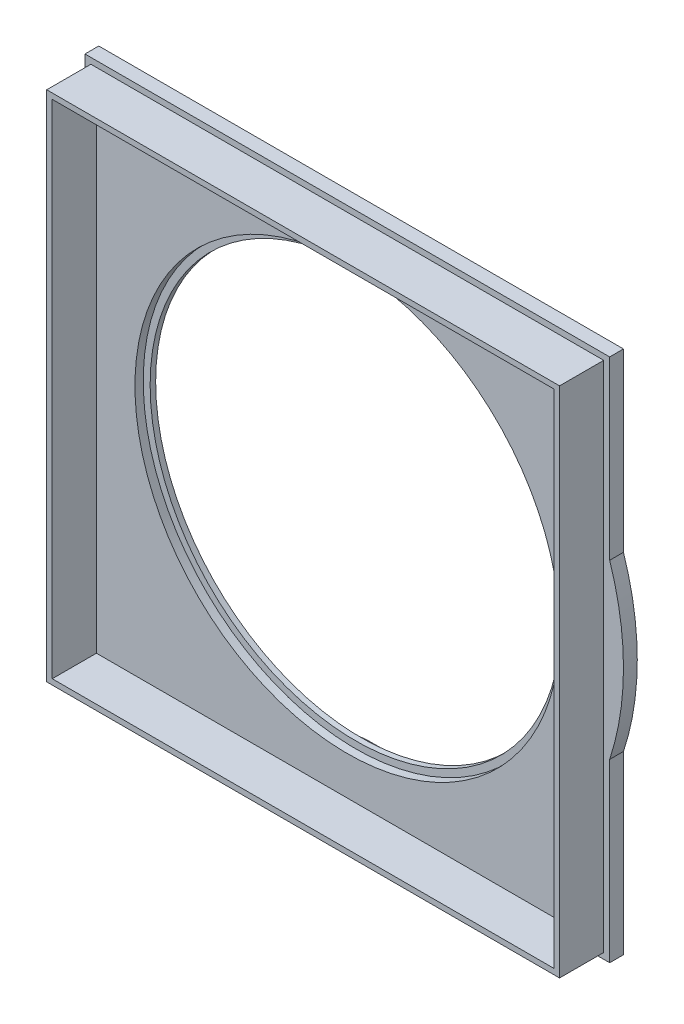
SolidWorks part; units mm, degrees
ref_plane "Alzado" through (0, 0, 0) normal (0, 0, 1) x (1, 0, 0)
ref_plane "Planta" through (0, 0, 0) normal (0, 1, 0) x (1, 0, 0)
ref_plane "Vista lateral" through (0, 0, 0) normal (1, 0, 0) x (0, 0, -1)
sketch "Croquis1" plane through (0, 0, 0) normal (0, 0, 1) x (1, 0, 0)
  line L1 (-46.425, -46.425) -> (46.425, -46.425)
  line L2 (-46.425, -46.425) -> (-46.425, 46.425)
  line L3 (-46.425, 46.425) -> (46.425, 46.425)
  line L4 (46.425, -46.425) -> (46.425, 46.425)
  line L5 (-46.425, -46.425) -> (46.425, 46.425) construction
  line L6 (-46.425, 46.425) -> (46.425, -46.425) construction
  circle A0 centre (0, 0) radius 37.2
  point P0 (0, 0)
  dimension "D2" = 74.4
  dimension "D1" = 92.85
extrude "Saliente-Extruir1" add sketch "Croquis1" along normal blind 2.5
sketch "Croquis2" plane through (0, 0, 2.5) normal (0, 0, 1) x (1, 0, 0)
  line L4 (45.425, -45.425) -> (45.425, 45.425)
  line L5 (45.425, 45.425) -> (-45.425, 45.425)
  line L6 (-45.425, 45.425) -> (-45.425, -45.425)
  line L7 (-45.425, -45.425) -> (45.425, -45.425)
  line L8 (46.425, -46.425) -> (46.425, 46.425)
  line L9 (46.425, 46.425) -> (-46.425, 46.425)
  line L10 (-46.425, 46.425) -> (-46.425, -46.425)
  line L11 (-46.425, -46.425) -> (46.425, -46.425)
  line L12 (46.425, -46.425) -> (46.425, 46.425)
  line L13 (46.425, 46.425) -> (-46.425, 46.425)
  line L14 (-46.425, 46.425) -> (-46.425, -46.425)
  line L15 (-46.425, -46.425) -> (46.425, -46.425)
  dimension "D1" = 0
  dimension "D2" = 1
extrude "Saliente-Extruir2" add sketch "Croquis2" along normal blind 8
sketch "Croquis3" plane through (0, 0, 0) normal (0, 0, -1) x (-1, 0, 0)
  line L4 (-47.5, 15.6125) -> (-47.5, 47.5)
  line L5 (-47.5, -47.5) -> (47.5, -47.5)
  line L6 (-47.5, -47.5) -> (-47.5, -15.6125)
  line L7 (-47.5, 47.5) -> (47.5, 47.5)
  line L8 (47.5, -47.5) -> (47.5, -15.6125)
  line L9 (-47.5, -47.5) -> (47.5, 47.5) construction
  line L10 (-47.5, 47.5) -> (47.5, -47.5) construction
  line L11 (47.5, 15.6125) -> (47.5, 47.5)
  arc A0 (-47.5, 15.6125) -> (-47.5, -15.6125) centre (0, 0) ccw
  arc A1 (47.5, -15.6125) -> (47.5, 15.6125) centre (0, 0) ccw
  circle A2 centre (0, 0) radius 37.2
  point P2 (0, 0)
  dimension "D2" = 100
  dimension "D1" = 95
  dimension "D3" = 95
extrude "Saliente-Extruir3" add sketch "Croquis3" against normal up to vertex (2.5 mm away)
sketch "Croquis4" plane through (0, 0, 2.5) normal (0, 0, 1) x (1, 0, 0)
  circle A0 centre (0, 0) radius 38.45
  dimension "D1" = 76.9
extrude "Cortar-Extruir1" cut sketch "Croquis4" against normal blind 1.5
sketch "Croquis6" plane through (0, 0, 0) normal (0, 0, -1) x (-1, 0, 0)
  line L0 (-43.1304, 37.6927) -> (46.5995, 37.6927) construction
  line L2 (-45.3156, -46.6937) -> (46.5995, -46.6937) construction
  text T0 "<b>ABRIR EN CASO</b>" font "Arial Rounded MT Bold" height 9
  text T1 "<b>DE EMERGENCIA</b>" font "Arial Rounded MT Bold" height 9
  point P3 (-45.3156, -46.6937)
  point P4 (-45.8727, -46.6937)
  point P5 (-43.1774, 37.1444)
  point P6 (-43.1304, 37.6927)
extrude "Saliente-Extruir4" add sketch "Croquis6" along normal blind 0.9
